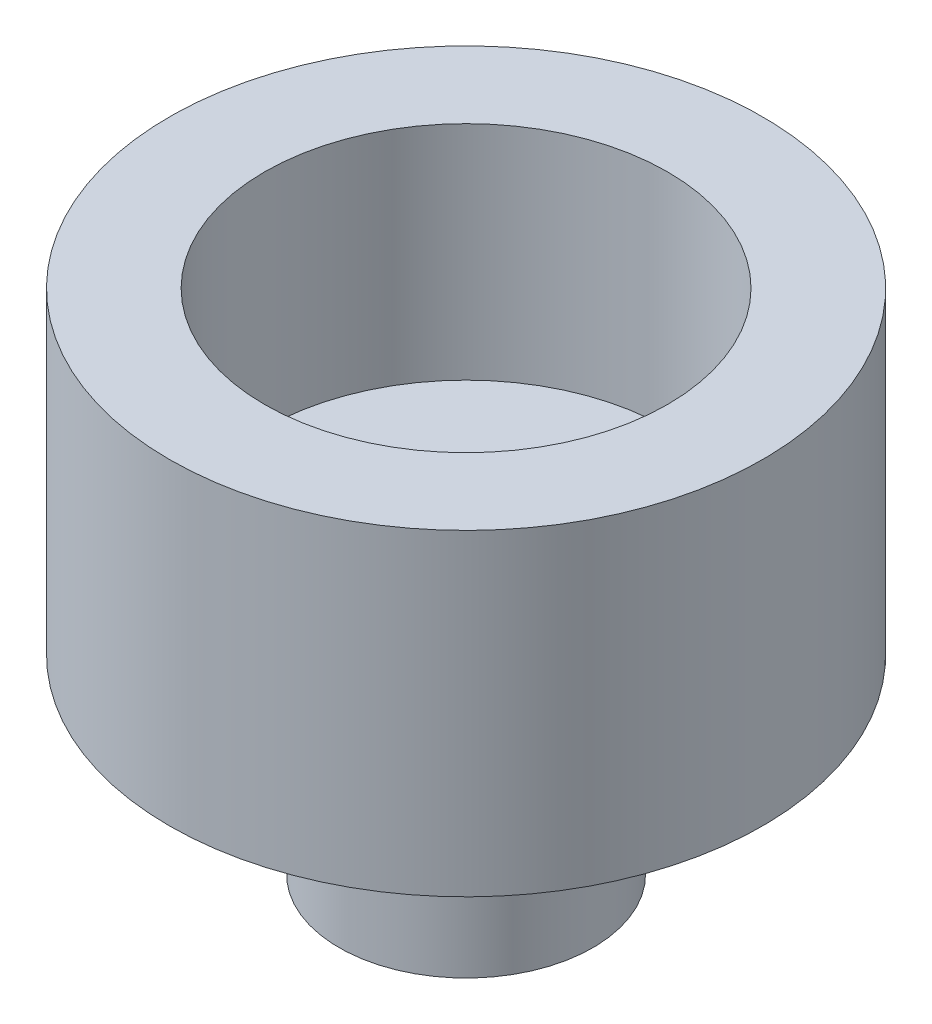
SolidWorks part; units mm, degrees
ref_plane "Front Plane" through (0, 0, 0) normal (0, 0, 1) x (1, 0, 0)
ref_plane "Top Plane" through (0, 0, 0) normal (0, 1, 0) x (1, 0, 0)
ref_plane "Right Plane" through (0, 0, 0) normal (1, 0, 0) x (0, 0, -1)
sketch "Sketch1" plane through (0, 0, 0) normal (0, 1, 0) x (1, 0, 0)
  circle A0 centre (0, 0) radius 9.35
  circle A1 centre (0, 0) radius 6.35 construction
  dimension "D1" = 12.7
  dimension "D2" = 3
extrude "Boss-Extrude1" add sketch "Sketch1" along normal blind 10
sketch "Sketch2" plane through (0, 10, 0) normal (0, 1, 0) x (1, 0, 0)
  circle A0 centre (0, 0) radius 6.35
  dimension "D1" = 12.7
extrude "Cut-Extrude1" cut sketch "Sketch2" against normal offset from surface (7 mm away) 3 up to face at (0, 0, 9.35)
sketch "Sketch3" plane through (0, 0, 0) normal (0, -1, 0) x (1, 0, 0)
  circle A0 centre (0, 0) radius 4
  dimension "D1" = 8
extrude "Boss-Extrude2" add sketch "Sketch3" along normal blind 6
